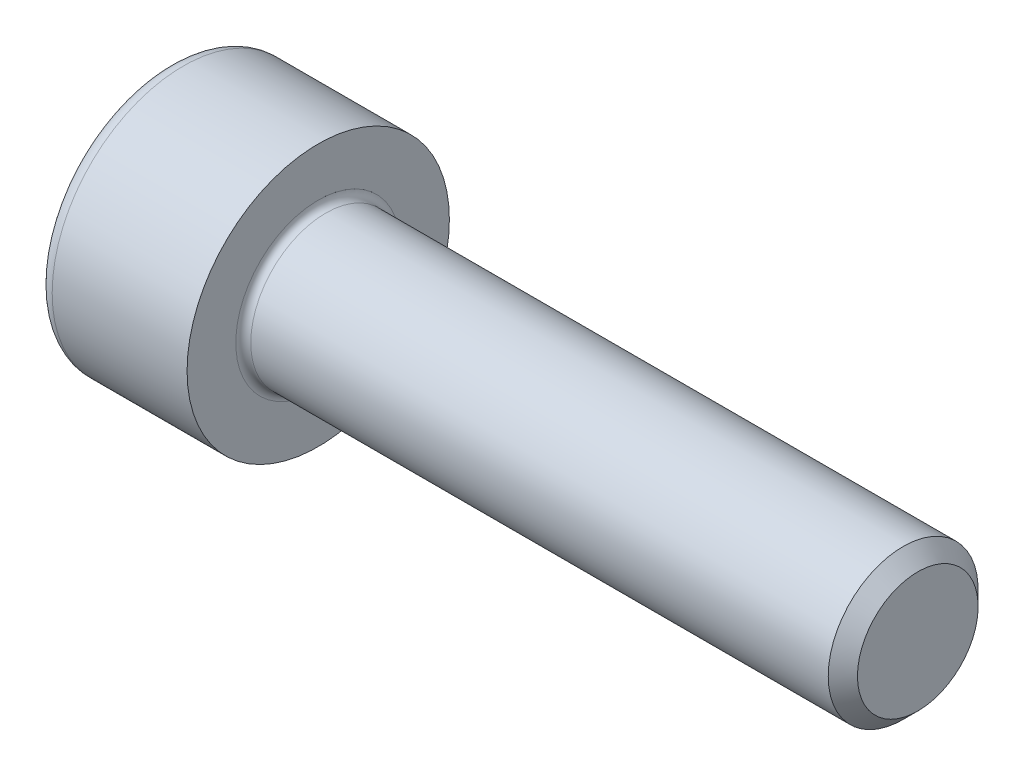
SolidWorks part; units mm, degrees
revolve "Base-Revolve" add sketch "BodySke"
sketch "BodySke" plane through (0, 0, 0) normal (0, 0, 1) x (1, 0, 0)
  line L0 (0, 0) -> (0, 3.5)
  line L1 (0, 3.5) -> (4, 3.5)
  line L2 (4, 3.5) -> (4, 2)
  line L3 (4, 2) -> (19.61, 2)
  line L4 (20, 1.61) -> (20, 0)
  line L5 (20, 0) -> (0, 0)
  line L6 (-31.75, 0) -> (127, 0) construction
  line L8 (20, 1.61) -> (19.61, 2)
  line L10 (20, -1.61) -> (19.61, -2) construction
  line L11 (4.7, 9.525) -> (4.7, 3.175) construction
  line L12 (4, 9.525) -> (4, 3.175) construction
  line L13 (-40, 9.525) -> (-40, 3.175) construction
  dimension "Head_ht" = 4
  dimension "Length" = 16
  dimension "Body_ch_ang" = 45
  dimension "Diameter" = 4
  dimension "Minor_dia" = 3.22
  dimension "Advance" = 0.7
  dimension "Thread_nom" = 16
  dimension "Thread_length" = 60
  dimension "Head_dia" = 7
cosmetic thread "ThreadCosmetic" [suppressed]
fillet "Fillet1" radius 0.2 1 edges at (4, 0, 2)
fillet "Fillet2" radius 0.4 1 edges at (0, 0, 3.5)
ref_plane "Plane1" through (0, 0, 0) normal (0, 0, 1) x (1, 0, 0)
ref_plane "Plane2" through (0, 0, 0) normal (0, 1, 0) x (1, 0, 0)
ref_plane "Plane3" through (0, 0, 0) normal (1, 0, 0) x (0, 0, -1)
other "Configuration Table"
sketch "Sketch2" plane through (0, 0, 0) normal (0, 0, 1) x (1, 0, 0)
  line L0 (0, 1.51) -> (2, 1.51)
  line L1 (2, 1.51) -> (2.8718, 0)
  line L2 (-31.75, 0) -> (127, 0) construction
  line L3 (2.8718, 0) -> (0, 0)
  line L4 (0, 0) -> (0, 1.51)
  line L6 (0, 0) -> (47.625, 0) construction
  dimension "D1" = 1.51
  dimension "D2" = 60
  dimension "Depth" = 2
revolve "Hex-PreBroach" cut sketch "Sketch2" angle 360 about L6
sketch "Sketch3" plane through (0, 0, 0) normal (-1, 0, 0) x (0, 0.5, 0.866)
  line L0 (0.8718, 1.51) -> (-0.8718, 1.51)
  line L1 (-0.8718, 1.51) -> (-1.7436, 0)
  line L2 (0.8718, 1.51) -> (1.7436, 0)
  line L3 (0.8718, -1.51) -> (1.7436, 0)
  line L4 (0.8718, -1.51) -> (-0.8718, -1.51)
  line L5 (-0.8718, -1.51) -> (-1.7436, 0)
  dimension "D1" = 1.51
  dimension "D2" = 1.51
  dimension "Hex_size" = 3.02
extrude "Hex" cut sketch "Sketch3" against normal blind 2
sketch "ThdSchSke" plane through (0, 0, 0) normal (0, 0, 1) x (1, 0, 0)
  line L0 (6.1, -1.61) -> (5.8269, -2)
  line L1 (6.1, -1.61) -> (6.3731, -2)
  line L2 (6.3731, -2) -> (6.3731, -2.5)
  line L3 (-3.175, 0) -> (5.1513, 0) construction
  line L4 (0, 3.1) -> (0, -3.1) construction
  line L5 (6.3731, -2.5) -> (5.8269, -2.5)
  line L6 (5.8269, -2.5) -> (5.8269, -2)
  dimension "Thread_minor" = 3.22
  dimension "Diameter" = 4
  dimension "Start" = 6.1
revolve "ThreadSchematic" [suppressed] cut sketch "ThdSchSke" angle 360 about L3
pattern_linear "ThdSchPat" [suppressed]
equation "\"D2@Sketch3\" = \"Hex_size@Sketch3\" / 2"
equation "\"D1@Sketch3\" = \"Hex_size@Sketch3\" / 2"
equation "\"D1@Sketch2\" = \"Hex_size@Sketch3\" / 2"
equation "\"Thread_minor@ThreadCosmetic\"  =  \"Minor_dia@BodySke\""
equation "\"Depth@Sketch2\" =  \"Key_eng@Hex\""
equation "\"Thread_length@ThreadCosmetic\" = ((sgn( (\"Length@BodySke\" - \"Advance@BodySke\" * 3.0) - \"Thread_nom@BodySke\" )-1)*( (\"Length@BodySke\" - \"Advance@BodySke\" * 3.0) - \"Thread_nom@BodySke\" ))/-2+ \"Thread_nom@BodySke\""
equation "\"Thread_minor@ThdSchSke\" = \"Minor_dia@BodySke\""
equation "\"Diameter@ThdSchSke\" = \"Diameter@BodySke\""
equation "\"Overcut@ThdSchSke\" = \"Diameter@BodySke\" * 1.25"
equation "\"Start@ThdSchSke\" = \"Head_ht@BodySke\" + \"Length@BodySke\" - \"Thread_length@ThreadCosmetic\"  '---Non-countersunk---"
equation "\"Num_threads@ThdSchPat\" = int( \"Thread_length@ThreadCosmetic\" / \"Advance@BodySke\" + 0.999 )  + 1"
equation "\"Advance@ThdSchPat\" = \"Thread_length@ThreadCosmetic\" /  (\"Num_threads@ThdSchPat\" - 1) 'relax it"
equation "\"Num_threads@ThdSchPat\" = \"Num_threads@ThdSchPat\" - sgn( \"Num_threads@ThdSchPat\" - 1) '---chamfered tips only---"
